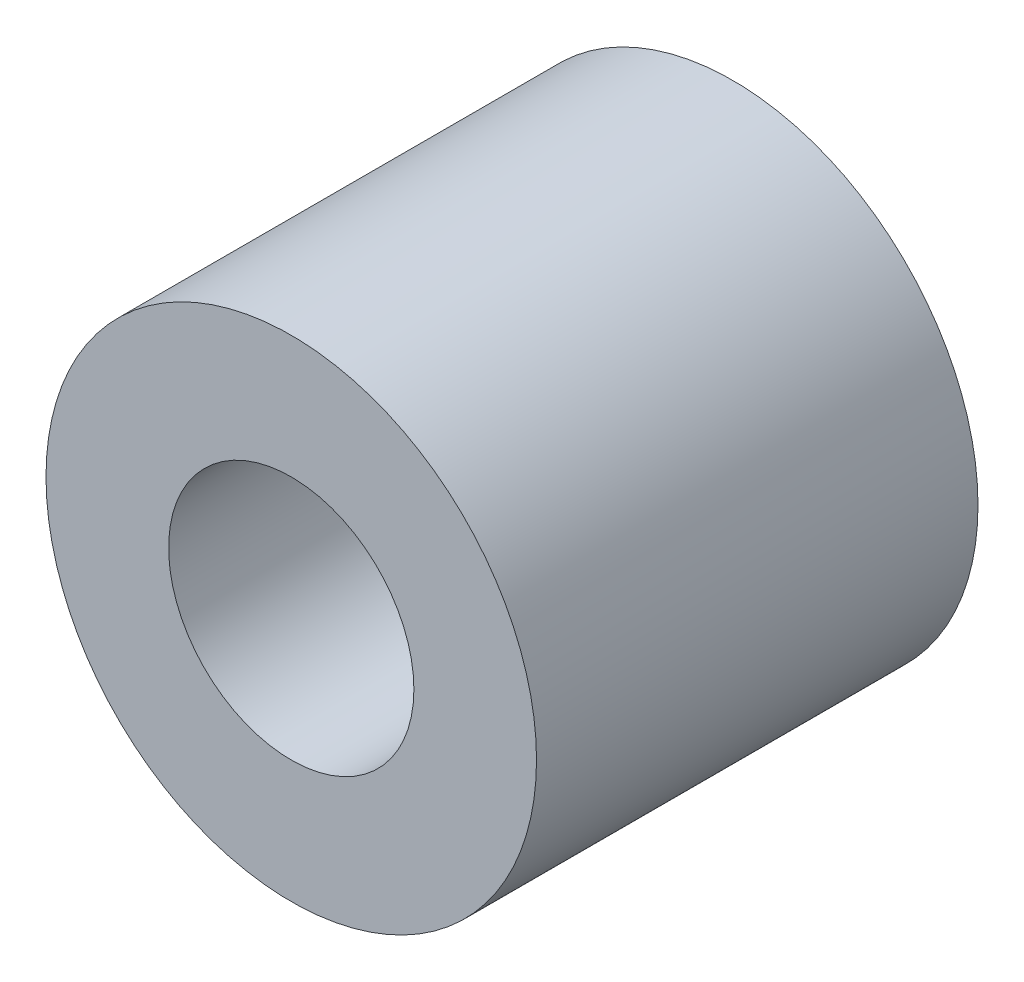
SolidWorks part; units mm, degrees
ref_plane "Plan de face" through (0, 0, 0) normal (0, 0, 1) x (1, 0, 0)
ref_plane "Plan de dessus" through (0, 0, 0) normal (0, 1, 0) x (1, 0, 0)
ref_plane "Plan de droite" through (0, 0, 0) normal (1, 0, 0) x (0, 0, -1)
sketch "Esquisse1" plane through (0, 0, 0) normal (0, 0, 1) x (1, 0, 0)
  circle A0 centre (0, 0) radius 5
  dimension "D1" = 10
extrude "Boss.-Extru.1" add sketch "Esquisse1" along normal blind 9 contours A0
sketch "Esquisse2" plane through (0, 0, 9) normal (0, 0, 1) x (1, 0, 0)
  circle A0 centre (0, 0) radius 2.5
  dimension "D1" = 5
extrude "Enlèv. mat.-Extru.1" cut sketch "Esquisse2" against normal blind 13
